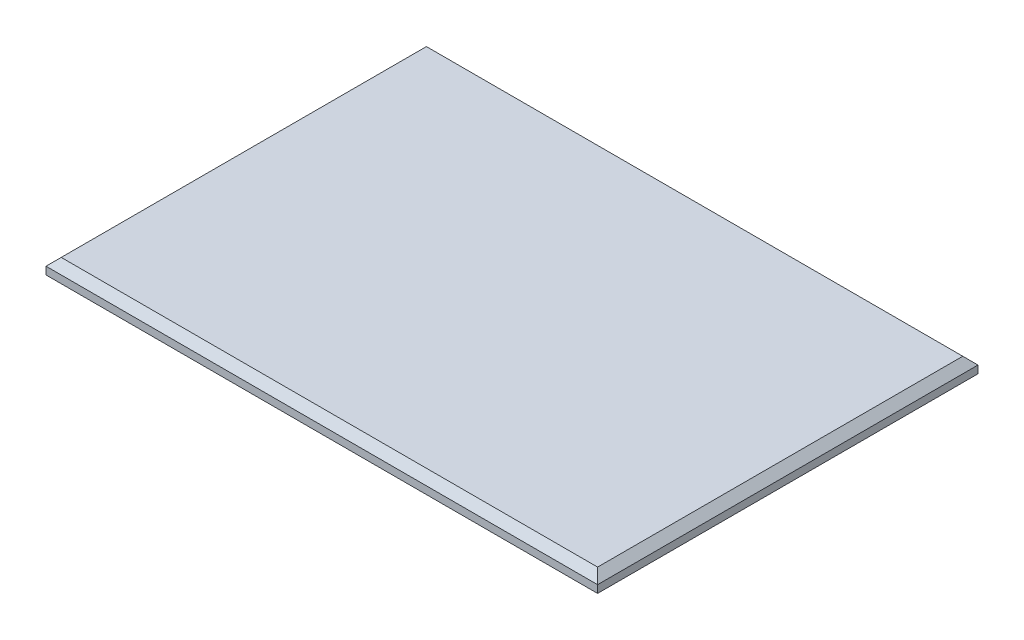
SolidWorks part; units mm, degrees
ref_plane "Front Plane" through (0, 0, 0) normal (0, 0, 1) x (1, 0, 0)
ref_plane "Top Plane" through (0, 0, 0) normal (0, 1, 0) x (1, 0, 0)
ref_plane "Right Plane" through (0, 0, 0) normal (1, 0, 0) x (0, 0, -1)
sketch "Sketch1" plane through (0, 0, 0) normal (0, 1, 0) x (1, 0, 0)
  line L1 (-72.5, 50) -> (72.5, 50)
  line L2 (-72.5, 50) -> (-72.5, -50)
  line L3 (-72.5, -50) -> (72.5, -50)
  line L4 (72.5, 50) -> (72.5, -50)
  line L5 (-72.5, 50) -> (72.5, -50) construction
  line L6 (-72.5, -50) -> (72.5, 50) construction
  point P0 (0, 0)
  dimension "D1" = 145
  dimension "D2" = 100
extrude "Boss-Extrude1" add sketch "Sketch1" along normal blind 4
chamfer "Chamfer2" distance 2 angle 45 4 edges at (0, 4, 50) (72.5, 4, 0) (0, 4, -50) (-72.5, 4, 0)
